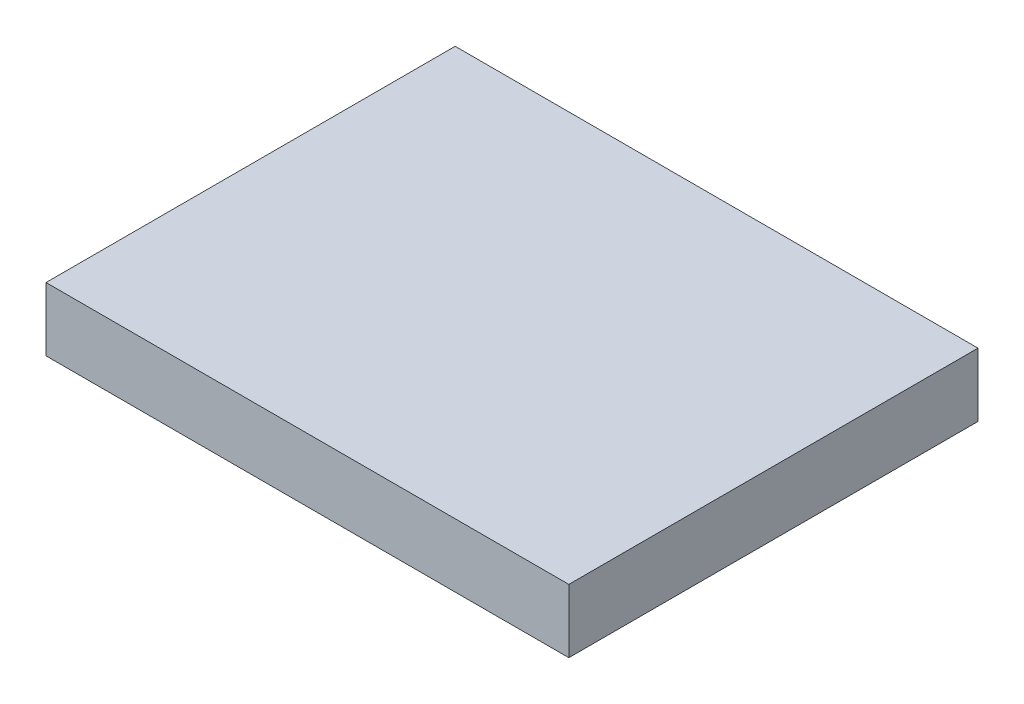
SolidWorks part; units mm, degrees
ref_plane "Front Plane" through (0, 0, 0) normal (0, 0, 1) x (1, 0, 0)
ref_plane "Top Plane" through (0, 0, 0) normal (0, 1, 0) x (1, 0, 0)
ref_plane "Right Plane" through (0, 0, 0) normal (1, 0, 0) x (0, 0, -1)
sketch "Sketch1" plane through (0, 0, 0) normal (0, 1, 0) x (1, 0, 0)
  line L1 (-34.5, 27) -> (34.5, 27)
  line L2 (-34.5, 27) -> (-34.5, -27)
  line L3 (-34.5, -27) -> (34.5, -27)
  line L4 (34.5, 27) -> (34.5, -27)
  line L5 (-34.5, 27) -> (34.5, -27) construction
  line L6 (-34.5, -27) -> (34.5, 27) construction
  point P0 (0, 0)
  dimension "D1" = 69
  dimension "D2" = 54
extrude "Boss-Extrude1" add sketch "Sketch1" along normal blind 8.382
